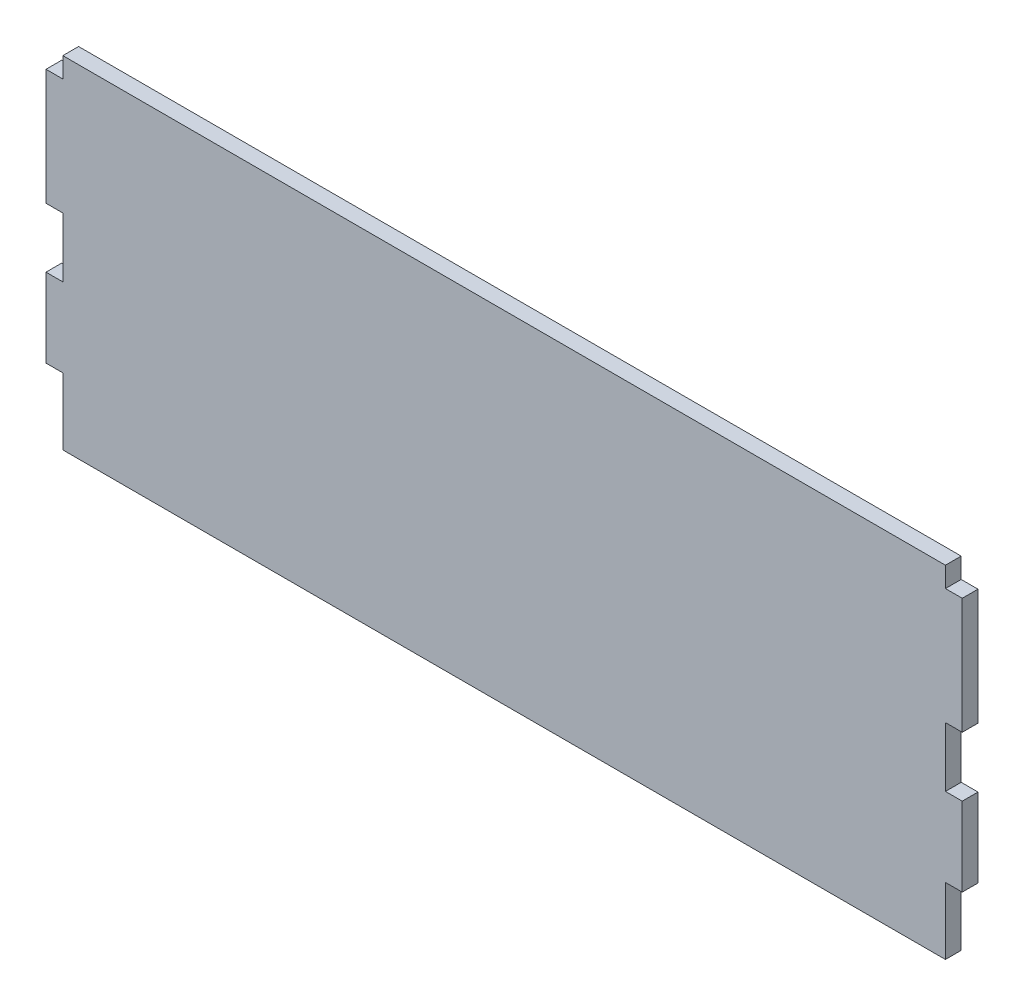
SolidWorks part; units mm, degrees
ref_plane "Alzado" through (0, 0, 0) normal (0, 0, 1) x (1, 0, 0)
ref_plane "Planta" through (0, 0, 0) normal (0, 1, 0) x (1, 0, 0)
ref_plane "Vista lateral" through (0, 0, 0) normal (1, 0, 0) x (0, 0, -1)
sketch "Croquis1" plane through (0, 0, 0) normal (0, 0, 1) x (1, 0, 0)
  line L0 (-84, 37.2954) -> (-87.2, 37.2954)
  line L1 (84, -50) -> (-84, -50)
  line L2 (84, -50) -> (84, -37.2954)
  line L3 (84, 50) -> (-84, 50)
  line L4 (-84, -50) -> (-84, -37.2954)
  line L5 (84, -50) -> (-84, 50) construction
  line L6 (84, 50) -> (-84, -50) construction
  line L7 (-87.2, 37.2954) -> (-87.2, 22.2954)
  line L8 (-87.2, 22.2954) -> (-84, 22.2954)
  line L9 (-84, 37.2954) -> (-84, 50)
  line L10 (0, 50) -> (0, -50) construction
  line L11 (-84, 0) -> (84, 0) construction
  line L12 (-87.2, -22.2954) -> (-84, -22.2954)
  line L13 (-87.2, -37.2954) -> (-87.2, -22.2954)
  line L14 (-84, -37.2954) -> (-87.2, -37.2954)
  line L15 (84, -37.2954) -> (87.2, -37.2954)
  line L16 (87.2, -37.2954) -> (87.2, -22.2954)
  line L17 (87.2, -22.2954) -> (84, -22.2954)
  line L18 (87.2, 22.2954) -> (84, 22.2954)
  line L19 (87.2, 37.2954) -> (87.2, 22.2954)
  line L20 (84, 37.2954) -> (87.2, 37.2954)
  line L21 (84, 37.2954) -> (84, 50)
  line L22 (84, -22.2954) -> (84, -10.9454)
  line L23 (-84, -22.2954) -> (-84, -10.9454)
  line L24 (-84, 11.1479) -> (-87.2, 11.1479)
  line L25 (-87.2, 11.1479) -> (-87.2, -10.9454)
  line L26 (-87.2, -10.9454) -> (-84, -10.9454)
  line L27 (-84, 11.1479) -> (-84, 22.2954)
  line L28 (87.2, -10.9454) -> (84, -10.9454)
  line L29 (87.2, 11.1479) -> (87.2, -10.9454)
  line L30 (84, 11.1479) -> (87.2, 11.1479)
  line L31 (84, 11.1479) -> (84, 22.2954)
  point P0 (0, 0)
  dimension "D1" = 168
  dimension "D2" = 100
  dimension "D3" = 3.2
  dimension "D4" = 15
  dimension "D5" = 12.7046
  dimension "D6" = 44.5908
  dimension "D7" = 11.1475
  dimension "D8" = 11.35
  dimension "D9" = 87.2
extrude "Saliente-Extruir1" add sketch "Croquis1" along normal blind 3
sketch "Croquis2" plane through (0, 0, 3) normal (0, 0, 1) x (1, 0, 0)
  line L0 (84, 50) -> (-84, 50) construction
  line L1 (-90.7019, 50) -> (109.1434, 50)
  line L2 (-90.7019, 50) -> (-90.7019, 14.9988)
  line L3 (-90.7019, 14.9988) -> (109.1434, 14.9988)
  line L4 (109.1434, 50) -> (109.1434, 14.9988)
  dimension "D1" = 35.0012
  dimension "D2" = 0
extrude "Cortar-Extruir1" cut sketch "Croquis2" against normal through all
